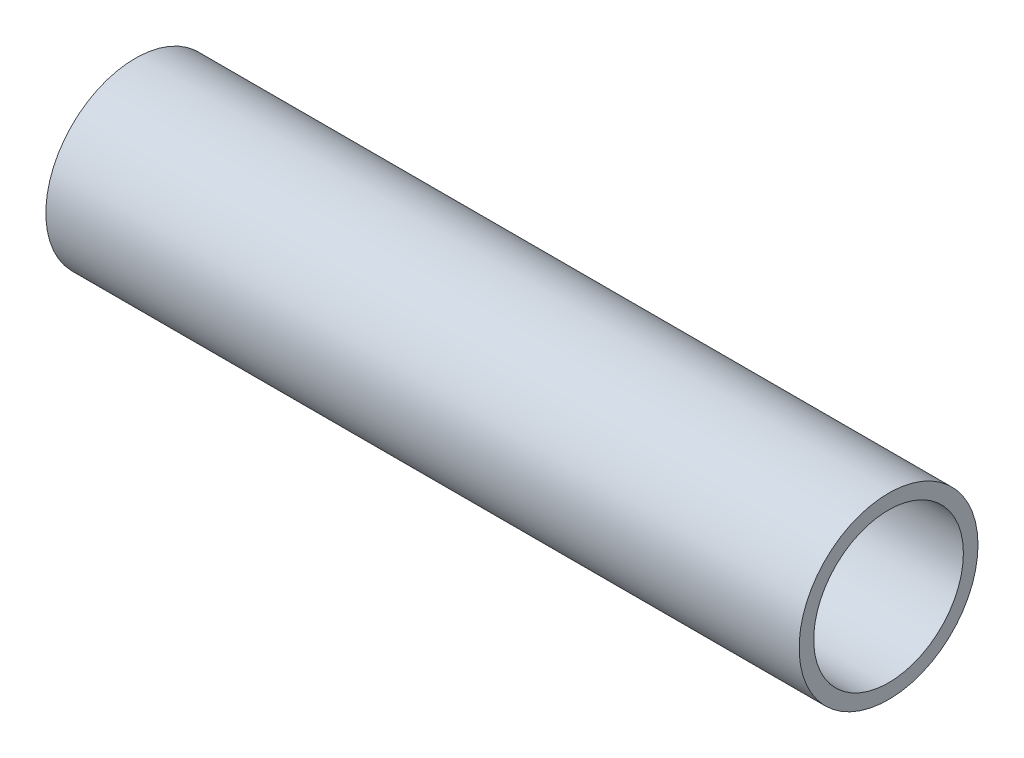
SolidWorks part; units mm, degrees
material "PVC Rigid"
ref_plane "Front Plane" through (0, 0, 0) normal (0, 0, 1) x (1, 0, 0)
ref_plane "Top Plane" through (0, 0, 0) normal (0, 1, 0) x (1, 0, 0)
ref_plane "Right Plane" through (0, 0, 0) normal (1, 0, 0) x (0, 0, -1)
sketch "Sketch1" plane through (0, 0, 0) normal (1, 0, 0) x (0, 0, -1)
  circle A0 centre (0, 0) radius 24.13
  circle A1 centre (0, 0) radius 20.193
  dimension "D1" = 48.26
  dimension "D2" = 40.386
extrude "Boss-Extrude1" add sketch "Sketch1" along normal blind 203.2
